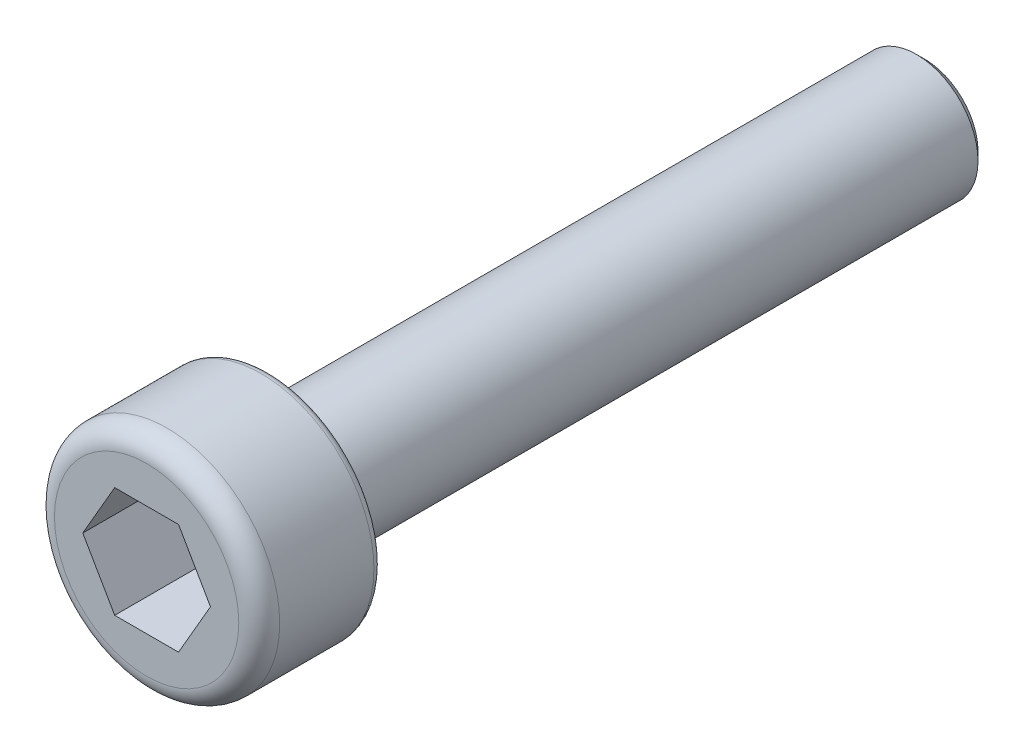
SolidWorks part; units mm, degrees
ref_plane "前视" through (0, 0, 0) normal (0, 0, 1) x (1, 0, 0)
ref_plane "上视" through (0, 0, 0) normal (0, 1, 0) x (1, 0, 0)
ref_plane "右视" through (0, 0, 0) normal (1, 0, 0) x (0, 0, -1)
sketch "草图1" plane through (0, 0, 0) normal (0, 0, 1) x (1, 0, 0)
  circle A0 centre (0, 0) radius 2.75
  dimension "D1" = 5.5
extrude "凸台-拉伸1" add sketch "草图1" along normal blind 3
fillet "圆角1" radius 0.5 1 edges at (2.75, 0, 3)
sketch "草图2" plane through (0, 0, 3) normal (0, 0, 1) x (1, 0, 0)
  line L1 (1.5588, 0) -> (0.7794, 1.35)
  line L2 (0.7794, 1.35) -> (-0.7794, 1.35)
  line L3 (-0.7794, 1.35) -> (-1.5588, 0)
  line L4 (-1.5588, 0) -> (-0.7794, -1.35)
  line L5 (-0.7794, -1.35) -> (0.7794, -1.35)
  line L6 (0.7794, -1.35) -> (1.5588, 0)
  circle A0 centre (0, 0) radius 1.35 construction
  dimension "D1" = 2.7
extrude "切除-拉伸1" cut sketch "草图2" against normal blind 2
sketch "草图3" plane through (0, 0, 0) normal (0, 0, -1) x (-1, 0, 0)
  circle A0 centre (0, 0) radius 1.5
  dimension "D1" = 3
extrude "凸台-拉伸2" add sketch "草图3" along normal blind 16
chamfer "倒角1" distance 0.2 angle 45 1 edges at (-1.5, 0, -16)
fillet "圆角2" radius 0.2 1 edges at (2.75, 0, 0)
